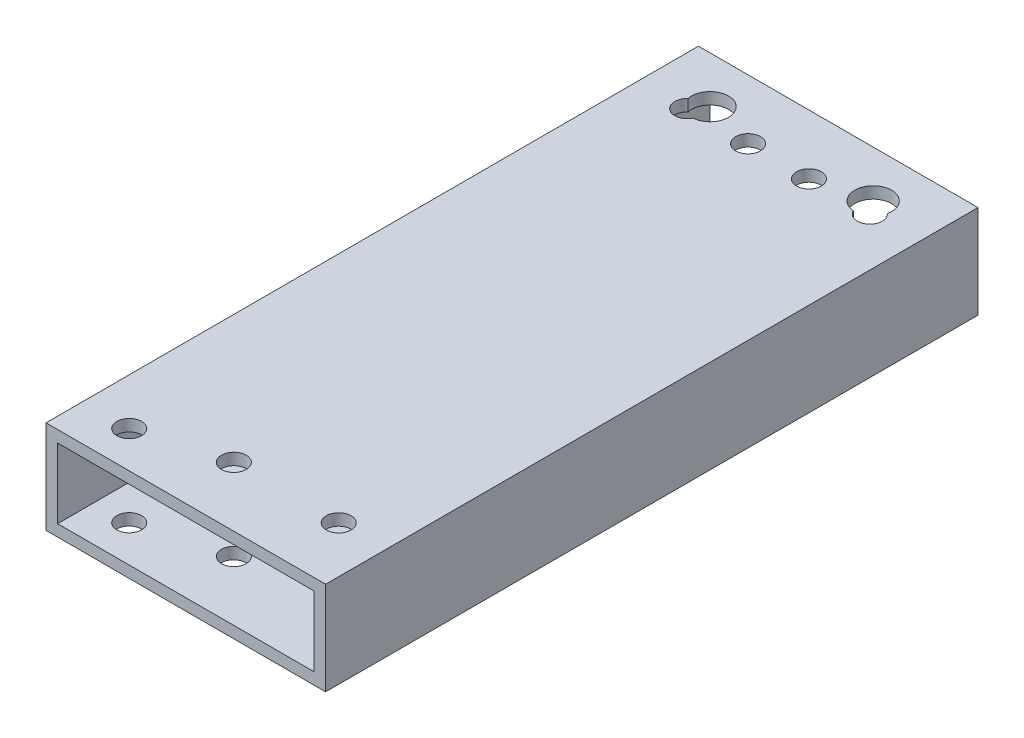
SolidWorks part; units mm, degrees
material "6061-T6 (SS)"
ref_plane "Front Plane" through (0, 0, 0) normal (0, 0, 1) x (1, 0, 0)
ref_plane "Top Plane" through (0, 0, 0) normal (0, 1, 0) x (1, 0, 0)
ref_plane "Right Plane" through (0, 0, 0) normal (1, 0, 0) x (0, 0, -1)
sketch "Sketch1" plane through (0, 0, 0) normal (0, 0, 1) x (1, 0, 0)
  line L0 (3.175, 3.175) -> (73.025, 3.175)
  line L1 (0, 0) -> (76.2, 0)
  line L2 (0, 0) -> (0, 25.4)
  line L3 (0, 25.4) -> (76.2, 25.4)
  line L4 (76.2, 0) -> (76.2, 25.4)
  line L5 (73.025, 3.175) -> (73.025, 22.225)
  line L6 (3.175, 22.225) -> (73.025, 22.225)
  line L7 (3.175, 3.175) -> (3.175, 22.225)
  dimension "D1" = 76.2
  dimension "D2" = 25.4
  dimension "D3" = 3.175
extrude "Boss-Extrude1" add sketch "Sketch1" along normal blind 177.8
sketch "Sketch2" plane through (0, 0, 0) normal (0, 0, -1) x (-1, 0, 0)
  line L0 (0, 0) -> (0, 127) construction
  line L1 (-76.2, 0) -> (-76.2, 127) construction
  dimension "D1" = 127
  dimension "D2" = 127
sketch "Sketch4" plane through (0, 25.4, 0) normal (0, 1, 0) x (1, 0, 0)
  circle A0 centre (13.2131, -16.2687) radius 3.3782
  circle A1 centre (29.8044, -16.2687) radius 3.3782
  circle A2 centre (46.3956, -16.2687) radius 3.3782
  circle A3 centre (62.9869, -16.2687) radius 3.3782
  dimension "D1" = 6.7564
  dimension "D2" = 6.7564
  dimension "D3" = 6.7564
  dimension "D4" = 6.7564
extrude "Cut-Extrude1" cut sketch "Sketch4" against normal through all
sketch "Sketch5" plane through (0, 0, 0) normal (0, -1, 0) x (1, 0, 0)
  circle A0 centre (12.7, 167.8195) radius 3.3782
  dimension "D1" = 6.7564
extrude "Cut-Extrude2" cut sketch "Sketch5" against normal through all
sketch "Sketch6" plane through (0, 25.4, 0) normal (0, 1, 0) x (1, 0, 0)
  circle A0 centre (63.5, -161.5313) radius 3.3782
  circle A1 centre (34.925, -161.5313) radius 3.3782
  dimension "D1" = 6.7564
  dimension "D2" = 6.7564
extrude "Cut-Extrude3" cut sketch "Sketch6" against normal through all
sketch "Sketch7" plane through (0, 0, 0) normal (0, -1, 0) x (1, 0, 0)
  line L0 (0, 0) -> (76.2, 0) construction
  line L1 (76.2, 177.8) -> (76.2, 0) construction
  circle A0 centre (15.875, 12.7) radius 5.0419
  circle A1 centre (60.325, 12.7) radius 5.0419
  dimension "D1" = 10.0838
  dimension "D2" = 10.0838
  dimension "D3" = 12.7
  dimension "D4" = 12.7
  dimension "D5" = 44.45
  dimension "D6" = 15.875
extrude "Cut-Extrude4" cut sketch "Sketch7" against normal through all
